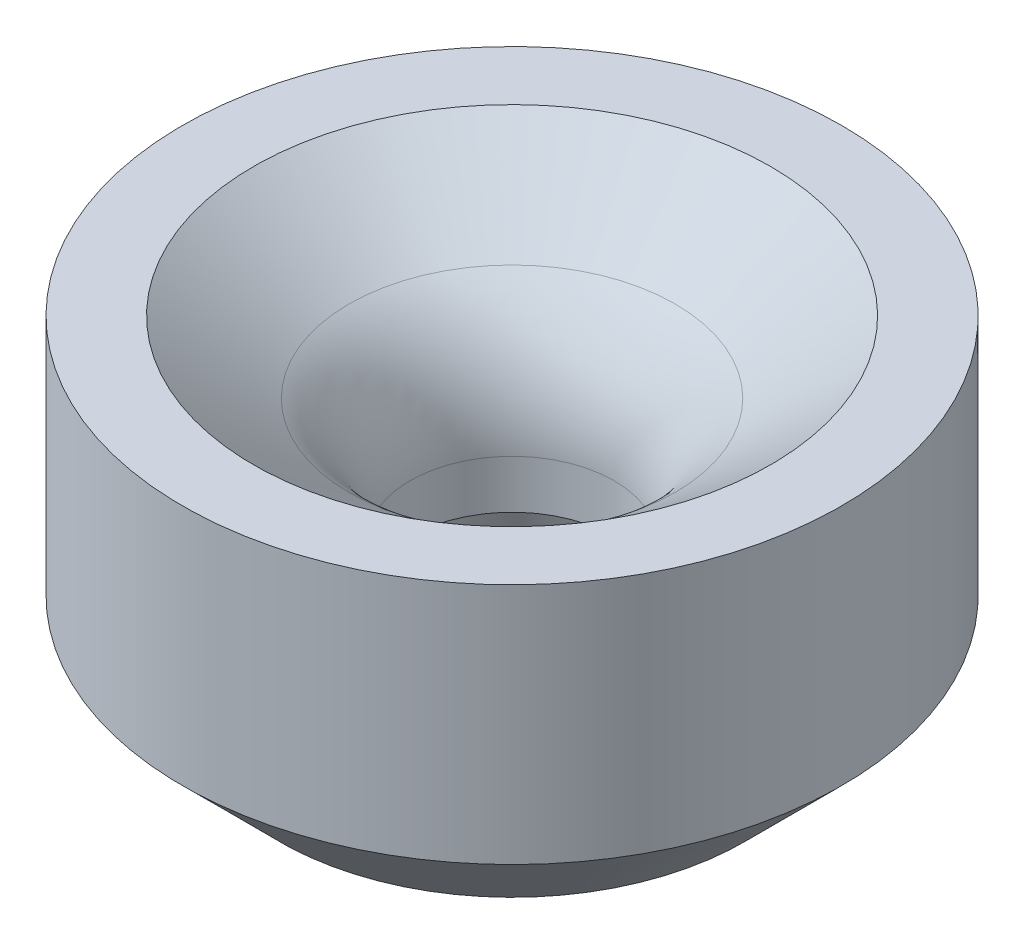
SolidWorks part; units mm, degrees
material "C (Graphite)"
ref_plane "Front Plane" through (0, 0, 0) normal (0, 0, 1) x (1, 0, 0)
ref_plane "Top Plane" through (0, 0, 0) normal (0, 1, 0) x (1, 0, 0)
ref_plane "Right Plane" through (0, 0, 0) normal (1, 0, 0) x (0, 0, -1)
sketch "Sketch1" plane through (0, 0, 0) normal (0, 0, 1) x (1, 0, 0)
  line L12 (-16.9333, 12.7) -> (-10.6883, 8.0162)
  line L14 (-6.6802, 0) -> (0, 0) construction
  line L15 (0, 0) -> (0, 24.638) construction
  line L21 (-21.59, -3.175) -> (-15.24, -9.525)
  line L23 (-6.6802, 0) -> (-6.6802, -3.175)
  line L25 (-8.6216, -9.525) -> (-15.24, -9.525)
  line L26 (-6.6802, -3.175) -> (-8.6216, -9.525)
  line L27 (-21.59, -3.175) -> (-21.59, 12.7)
  line L28 (-21.59, 12.7) -> (-16.9333, 12.7)
  arc A1 (-6.6802, 0) -> (-10.6883, 8.0162) centre (-16.7005, 0) ccw
  dimension "D14" = 10.0203
  dimension "D2" = 53.13
  dimension "D3" = 6.6802
  dimension "D4" = 21.59
  dimension "D5" = 45
  dimension "D6" = 22.225
  dimension "D7" = 6.35
  dimension "D8" = 17
  dimension "D9" = 6.35
  dimension "D10" = 3.175
revolve "Revolve1" add sketch "Sketch1" angle 360 about L15
